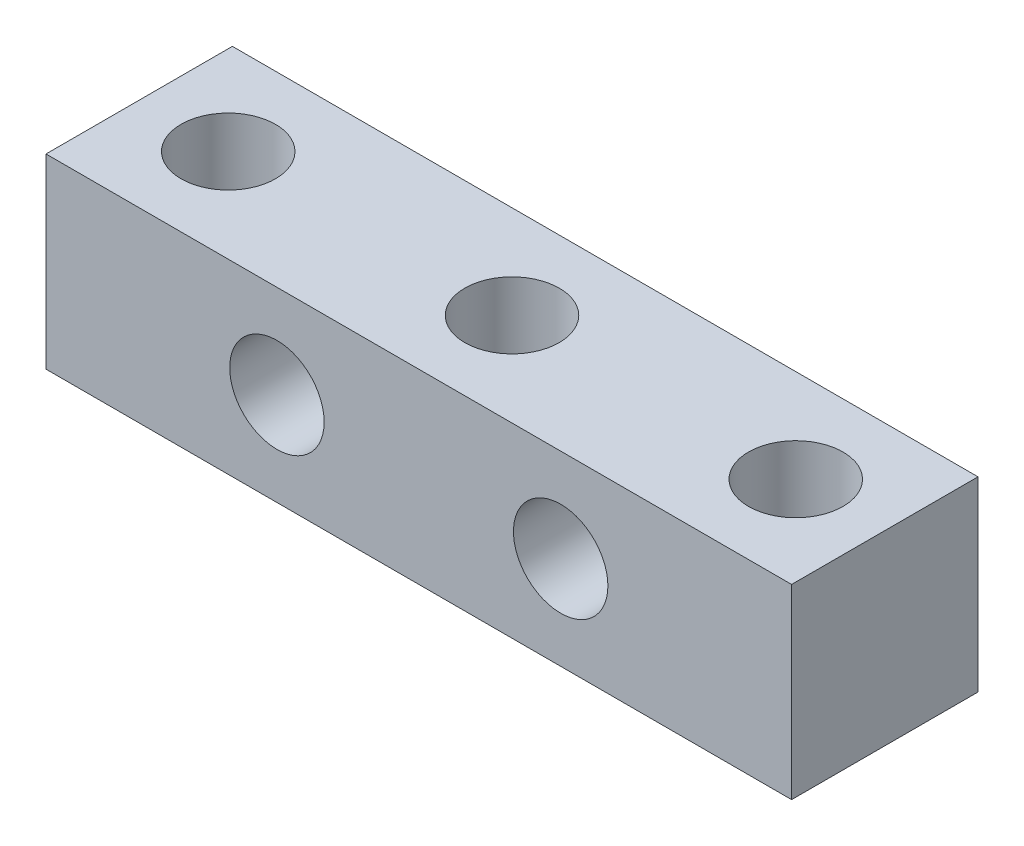
SolidWorks part; units mm, degrees
material "6061-T6 (SS)"
ref_plane "Front Plane" through (0, 0, 0) normal (0, 0, 1) x (1, 0, 0)
ref_plane "Top Plane" through (0, 0, 0) normal (0, 1, 0) x (1, 0, 0)
ref_plane "Right Plane" through (0, 0, 0) normal (1, 0, 0) x (0, 0, -1)
sketch "Sketch1" plane through (0, 0, 0) normal (1, 0, 0) x (0, 0, -1)
  line L1 (-4.7625, 4.7625) -> (4.7625, 4.7625)
  line L2 (-4.7625, 4.7625) -> (-4.7625, -4.7625)
  line L3 (-4.7625, -4.7625) -> (4.7625, -4.7625)
  line L4 (4.7625, 4.7625) -> (4.7625, -4.7625)
extrude "Boss-Extrude1" add sketch "Sketch1" along normal blind 38.1
hole_wizard "#10-24 Tapped Hole1" positions "Sketch3" profile "Sketch2" tap size "#10-24" standard "ANSI Inch" end condition through all
sketch "Sketch3" plane through (0, 4.7625, 0) normal (0, 1, 0) x (1, 0, 0)
  line L0 (19.05, 4.7625) -> (19.05, 0) construction
  line L1 (38.1, 4.7625) -> (0, 4.7625) construction
  point P0 (4.55, 0)
  point P2 (19.05, 0)
  point P4 (33.55, 0)
  dimension "D1" = 14.5
  dimension "D2" = 14.5
sketch "Sketch2" plane through (4.55, 4.7625, 0) normal (1, 0, 0) x (0, 0, 1)
  line L0 (0, 0) -> (0, 9.525)
  line L1 (0, 9.525) -> (2.413, 9.525)
  line L2 (2.413, 9.525) -> (2.413, 0)
  line L5 (2.413, 0) -> (0, 0)
  line L11 (0, -6.35) -> (0, 107.95) construction
  dimension "Thread Major Dia." = 4.826
  dimension "Thru Tap Drill Depth" = 9.525
hole_wizard "#10-24 Tapped Hole2" positions "Sketch5" profile "Sketch4" tap size "#10-24" standard "ANSI Inch" end condition through all
sketch "Sketch5" plane through (0, 0, 4.7625) normal (0, 0, 1) x (1, 0, 0)
  line L0 (19.05, 4.7625) -> (19.05, -4.7625) construction
  line L1 (38.1, 4.7625) -> (0, 4.7625) construction
  line L2 (38.1, -4.7625) -> (0, -4.7625) construction
  point P0 (11.8, 0)
  point P2 (26.3, 0)
  dimension "D1" = 7.25
  dimension "D2" = 7.25
sketch "Sketch4" plane through (11.8, 0, 4.7625) normal (1, 0, 0) x (0, -1, 0)
  line L0 (0, 0) -> (0, 9.525)
  line L1 (0, 9.525) -> (2.413, 9.525)
  line L2 (2.413, 9.525) -> (2.413, 0)
  line L5 (2.413, 0) -> (0, 0)
  line L11 (0, -6.35) -> (0, 107.95) construction
  dimension "Thread Major Dia." = 4.826
  dimension "Thru Tap Drill Depth" = 9.525
